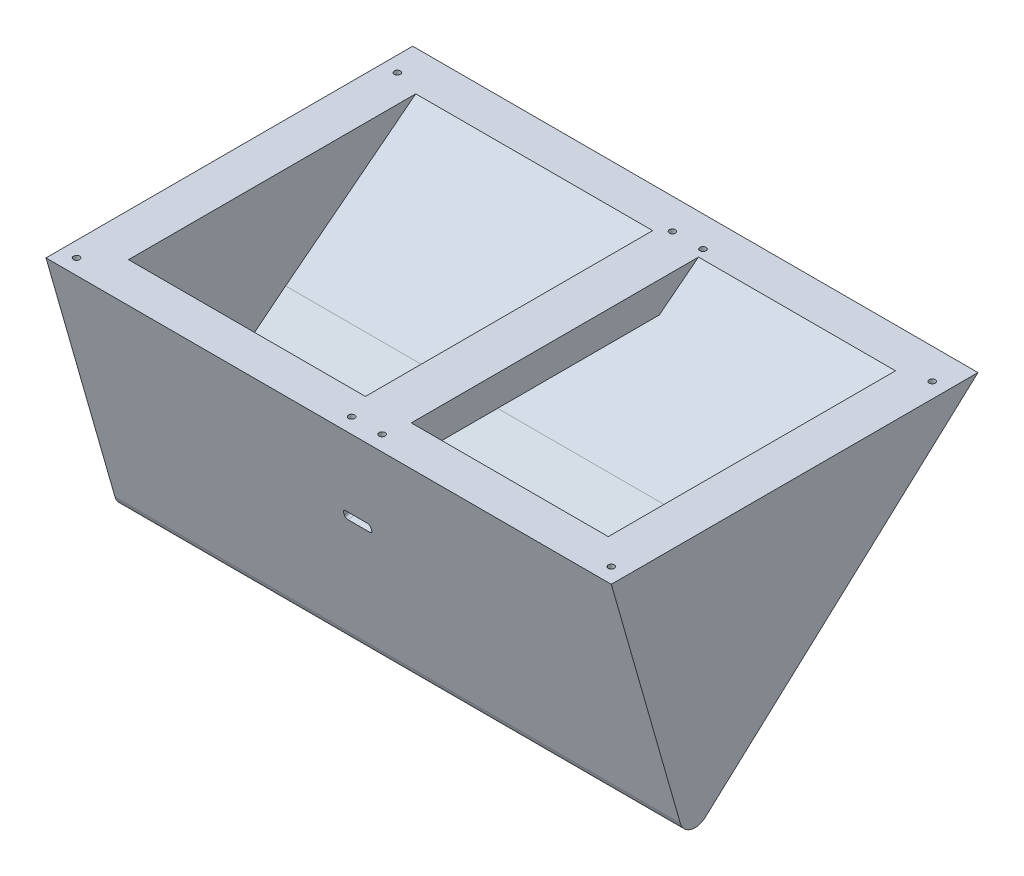
SolidWorks part; units mm, degrees
ref_plane "Front Plane" through (0, 0, 0) normal (0, 0, 1) x (1, 0, 0)
ref_plane "Top Plane" through (0, 0, 0) normal (0, 1, 0) x (1, 0, 0)
ref_plane "Right Plane" through (0, 0, 0) normal (1, 0, 0) x (0, 0, -1)
sketch "Sketch1" plane through (0, 0, 0) normal (0, 1, 0) x (1, 0, 0)
  line L1 (-92.5, -60) -> (92.5, -60)
  line L2 (-92.5, -60) -> (-92.5, 60)
  line L3 (-92.5, 60) -> (92.5, 60)
  line L4 (92.5, -60) -> (92.5, 60)
  line L5 (-92.5, -60) -> (92.5, 60) construction
  line L6 (-92.5, 60) -> (92.5, -60) construction
  point P0 (0, 0)
  dimension "D1" = 185
  dimension "D2" = 120
extrude "Boss-Extrude1" add sketch "Sketch1" along normal blind 10
sketch "Sketch3" plane through (92.5, 0, 0) normal (1, 0, 0) x (0, 0, -1)
  line L0 (60, 0) -> (-35.1958, -86.8292)
  line L1 (-35.1958, -86.8292) -> (-60, 0)
  line L2 (-60, 0) -> (60, 0)
extrude "Boss-Extrude2" add sketch "Sketch3" against normal blind 14
sketch "Sketch4" plane through (78.5, 0, 0) normal (-1, 0, 0) x (0, 0, 1)
  line L0 (-12.4021, -43.4146) -> (-4.4155, -33.1572) construction
  line L1 (35.1958, -86.8292) -> (-60, 0) construction
  line L2 (47.5979, -43.4146) -> (35.1419, -39.6935) construction
  line L3 (60, 0) -> (35.1958, -86.8292) construction
  line L4 (35.1419, -39.6935) -> (47, 0)
  line L5 (-60, 0) -> (60, 0) construction
  line L6 (-4.4155, -33.1572) -> (-47, 0)
  line L7 (-4.4155, -33.1572) -> (31.436, -61.6146)
  line L8 (31.436, -61.6146) -> (35.1419, -39.6935)
  line L9 (-47, 0) -> (-60, 0)
  line L10 (-60, 0) -> (35.1958, -86.8292)
  line L11 (35.1958, -86.8292) -> (60, 0)
  line L12 (60, 0) -> (47, 0)
  dimension "D1" = 13
  dimension "D2" = 13
  dimension "D3" = 13
  dimension "D4" = 13
extrude "Boss-Extrude3" add sketch "Sketch4" along normal blind 157
sketch "Sketch5" plane through (-78.5, 0, 0) normal (-1, 0, 0) x (0, 0, 1)
  line L0 (60, 0) -> (-60, 0)
  line L1 (-60, 0) -> (35.1958, -86.8292)
  line L2 (35.1958, -86.8292) -> (60, 0)
extrude "Boss-Extrude4" add sketch "Sketch5" along normal blind 14
sketch "Sketch6" plane through (-92.5, 0, 0) normal (-1, 0, 0) x (0, 0, 1)
  line L0 (60, 0) -> (-60, 0)
  line L1 (-60, 0) -> (-60, 10)
  line L2 (-60, 10) -> (60, 10)
  line L3 (60, 10) -> (60, 0)
extrude "Cut-Extrude1" cut sketch "Sketch6" against normal blind 300
sketch "Sketch7" plane through (0, 0, 0) normal (0, 1, 0) x (1, 0, 0)
  line L1 (-78.5, -47) -> (78.5, -47) construction
  line L2 (-0.9681, -47) -> (-0.9681, 47)
  line L3 (-78.5, 47) -> (78.5, 47) construction
  line L4 (14.0319, 47) -> (-0.9681, 47)
  line L5 (14.0319, 47) -> (14.0319, -47)
  line L6 (14.0319, -47) -> (-0.9681, -47)
  point P6 (0, 0)
  dimension "D1" = 15
extrude "Boss-Extrude5" add sketch "Sketch7" against normal blind 10
sketch "Sketch8" plane through (0, 0, 0) normal (0, 1, 0) x (1, 0, 0)
  line L0 (-92.5, -60) -> (92.5, -60) construction
  line L1 (92.5, 60) -> (92.5, -60) construction
  line L3 (-92.5, -60) -> (-92.5, 60) construction
  line L4 (87.5, -55) -> (12.5, -55) construction
  line L7 (-87.5, -55) -> (2.5, -55) construction
  circle A0 centre (87.5, -55) radius 1
  circle A1 centre (-87.5, -55) radius 1
  circle A4 centre (12.5, -55) radius 1
  circle A7 centre (2.5, -55) radius 1
  dimension "D1" = 5
  dimension "D2" = 5
  dimension "D3" = 5
  dimension "D4" = 5
  dimension "D9" = 2
  dimension "D10" = 2
  dimension "D14" = 2
  dimension "D18" = 2
  dimension "D13" = 75
  dimension "D15" = 90
extrude "Cut-Extrude2" cut sketch "Sketch8" against normal blind 4
sketch "Sketch9" plane through (0, 0, 0) normal (0, 1, 0) x (1, 0, 0)
  line L0 (92.5, 60) -> (-92.5, 60) construction
  line L2 (92.5, 60) -> (92.5, -60) construction
  line L3 (-87.5, 50) -> (2.5, 50) construction
  line L4 (87.5, 50) -> (12.5, 50) construction
  line L5 (-92.5, -60) -> (-92.5, 60) construction
  circle A0 centre (87.5, 50) radius 1
  circle A1 centre (-87.5, 50) radius 1
  circle A2 centre (12.5, 50) radius 1
  circle A3 centre (2.5, 50) radius 1
  dimension "D1" = 10
  dimension "D2" = 2
  dimension "D3" = 10
  dimension "D4" = 5
  dimension "D5" = 2
  dimension "D6" = 5
  dimension "D9" = 2
  dimension "D10" = 2
  dimension "D7" = 75
  dimension "D8" = 90
extrude "Cut-Extrude3" cut sketch "Sketch9" against normal blind 4
fillet "Fillet1" radius 5 1 edges at (0, -86.8292, 35.1958)
sketch "Sketch10" plane through (0, -15.8468, 55.4731) normal (0, -0.2747, 0.9615) x (1, 0, 0)
  line L0 (0, 16.4807) -> (0, -65.7537) construction
  line L1 (-92.5, 16.4807) -> (92.5, 16.4807) construction
  line L2 (-92.5, -65.7537) -> (92.5, -65.7537) construction
  line L3 (-92.5, -18.0266) -> (92.5, -18.0266) construction
  line L4 (-92.5, -65.7537) -> (-92.5, 16.4807) construction
  line L5 (92.5, 16.4807) -> (92.5, -65.7537) construction
  line L7 (-4.47, -19.6066) -> (4.47, -19.6066)
  line L8 (-4.47, -19.6066) -> (-4.47, -16.4466)
  line L9 (-4.47, -16.4466) -> (4.47, -16.4466)
  line L10 (4.47, -19.6066) -> (4.47, -16.4466)
  line L11 (-4.47, -19.6066) -> (4.47, -16.4466) construction
  line L12 (-4.47, -16.4466) -> (4.47, -19.6066) construction
  point P12 (0, -18.0266)
  dimension "D1" = 8.94
  dimension "D2" = 3.16
extrude "Cut-Extrude4" cut sketch "Sketch10" against normal blind 13
fillet "Fillet2" radius 1 4 edges at (-4.47, -32.9287, 43.8896) (4.47, -32.9287, 43.8896) (4.47, -29.8955, 44.7759) (-4.47, -29.8955, 44.7759)
sketch "Sketch12" plane through (0, -15.8468, 55.4731) normal (0, -0.2747, 0.9615) x (1, 0, 0)
  line L0 (-9.15, -19.6066) -> (9.15, -19.6066)
  line L2 (-9.15, -19.6066) -> (-9.15, -21.6066)
  line L3 (-9.15, -21.6066) -> (9.15, -21.6066)
  line L4 (9.15, -21.6066) -> (9.15, -19.6066)
  line L5 (-3.47, -19.6066) -> (3.47, -19.6066) construction
  point P3 (0, -19.6066)
  point P7 (0, -19.6066)
  dimension "D1" = 18.3
  dimension "D2" = 2
extrude "Cut-Extrude6" cut sketch "Sketch12" against normal blind 13
sketch "Sketch13" plane through (0, -15.8468, 55.4731) normal (0, -0.2747, 0.9615) x (1, 0, 0)
  line L1 (-9.15, -19.6066) -> (9.15, -19.6066)
  line L2 (-9.15, -19.6066) -> (-9.15, -21.6066)
  line L3 (-9.15, -21.6066) -> (9.15, -21.6066)
  line L4 (9.15, -19.6066) -> (9.15, -21.6066)
extrude "Boss-Extrude6" add sketch "Sketch13" against normal blind 7.89
